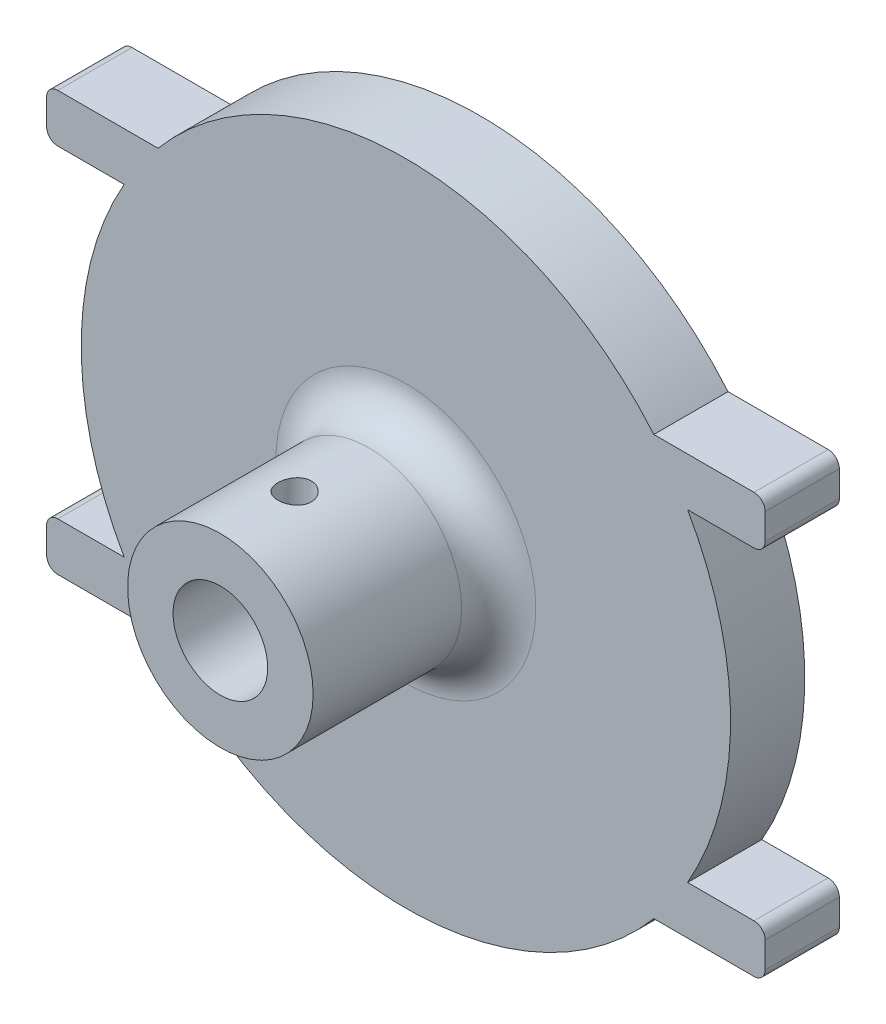
SolidWorks part; units mm, degrees
ref_plane "Front Plane" through (0, 0, 0) normal (0, 0, 1) x (1, 0, 0)
ref_plane "Top Plane" through (0, 0, 0) normal (0, 1, 0) x (1, 0, 0)
ref_plane "Right Plane" through (0, 0, 0) normal (1, 0, 0) x (0, 0, -1)
sketch "Sketch1" plane through (0, 0, 0) normal (0, 0, 1) x (1, 0, 0)
  line L0 (-23.8285, 14.351) -> (-16.9705, 14.351)
  line L1 (24.5905, 13.589) -> (24.5905, 11.811)
  line L2 (23.8285, 11.049) -> (19.2839, 11.049)
  line L3 (-24.5905, 11.811) -> (-24.5905, 13.589)
  line L4 (-19.2839, 11.049) -> (-23.8285, 11.049)
  line L5 (16.9705, 14.351) -> (23.8285, 14.351)
  line L6 (-22.225, 0) -> (22.225, 0) construction
  line L7 (23.8285, -11.049) -> (19.2839, -11.049)
  line L8 (24.5905, -13.589) -> (24.5905, -11.811)
  line L9 (16.9705, -14.351) -> (23.8285, -14.351)
  line L10 (-23.8285, -14.351) -> (-16.9705, -14.351)
  line L11 (-24.5905, -11.811) -> (-24.5905, -13.589)
  line L12 (-19.2839, -11.049) -> (-23.8285, -11.049)
  arc A0 (-19.2839, 11.049) -> (-19.2839, -11.049) centre (0, 0) ccw
  arc A1 (23.8285, 14.351) -> (24.5905, 13.589) centre (23.8285, 13.589) cw
  arc A2 (24.5905, 11.811) -> (23.8285, 11.049) centre (23.8285, 11.811) cw
  arc A3 (23.8285, -11.049) -> (24.5905, -11.811) centre (23.8285, -11.811) cw
  arc A4 (24.5905, -13.589) -> (23.8285, -14.351) centre (23.8285, -13.589) cw
  arc A5 (-23.8285, -14.351) -> (-24.5905, -13.589) centre (-23.8285, -13.589) cw
  arc A6 (-24.5905, -11.811) -> (-23.8285, -11.049) centre (-23.8285, -11.811) cw
  arc A7 (-23.8285, 11.049) -> (-24.5905, 11.811) centre (-23.8285, 11.811) cw
  arc A8 (-23.8285, 14.351) -> (-24.5905, 13.589) centre (-23.8285, 13.589) ccw
  arc A9 (-16.9705, -14.351) -> (16.9705, -14.351) centre (0, 0) ccw
  arc A10 (19.2839, -11.049) -> (19.2839, 11.049) centre (0, 0) ccw
  arc A11 (16.9705, 14.351) -> (-16.9705, 14.351) centre (0, 0) ccw
  point P23 (24.5905, 14.351)
  point P26 (24.5905, 11.049)
  point P29 (24.5905, -11.049)
  point P32 (24.5905, -14.351)
  point P35 (-24.5905, -14.351)
  point P38 (-24.5905, -11.049)
  point P41 (-24.5905, 11.049)
  point P44 (-24.5905, 14.351)
  dimension "D1" = 44.45
  dimension "D7" = 0.762
  dimension "D2" = 3.302
  dimension "D3" = 7.62
  dimension "D4" = 7.62
  dimension "D5" = 3.302
  dimension "D6" = 22.098
extrude "Boss-Extrude1" add sketch "Sketch1" along normal blind 5.08
sketch "Sketch5" plane through (0, 0, 0) normal (0, 0, -1) x (-1, 0, 0)
  circle A0 centre (0, 0) radius 9.6901
  dimension "D1" = 19.3802
extrude "Cut-Extrude2" cut sketch "Sketch5" against normal blind 2.54
sketch "Sketch6" plane through (0, 0, 5.08) normal (0, 0, 1) x (1, 0, 0)
  circle A0 centre (0, 0) radius 6.35
  circle A1 centre (0, 0) radius 3.2385
  dimension "D1" = 12.7
  dimension "D2" = 6.477
extrude "Boss-Extrude4" add sketch "Sketch6" along normal blind 12.7
fillet "Fillet1" radius 2.54 1 edges at (6.35, 0, 5.08)
ref_plane "Plane1" through (0, 6.35, 0) normal (0, 1, 0) x (1, 0, 0)
sketch "Sketch8" plane through (0, 6.35, 0) normal (0, 1, 0) x (1, 0, 0)
  line L0 (-6.35, -17.78) -> (6.35, -17.78) construction
  circle A0 centre (0, -12.7) radius 1.143
  dimension "D1" = 2.286
  dimension "D2" = 5.08
extrude "Cut-Extrude3" cut sketch "Sketch8" against normal blind 7.62
